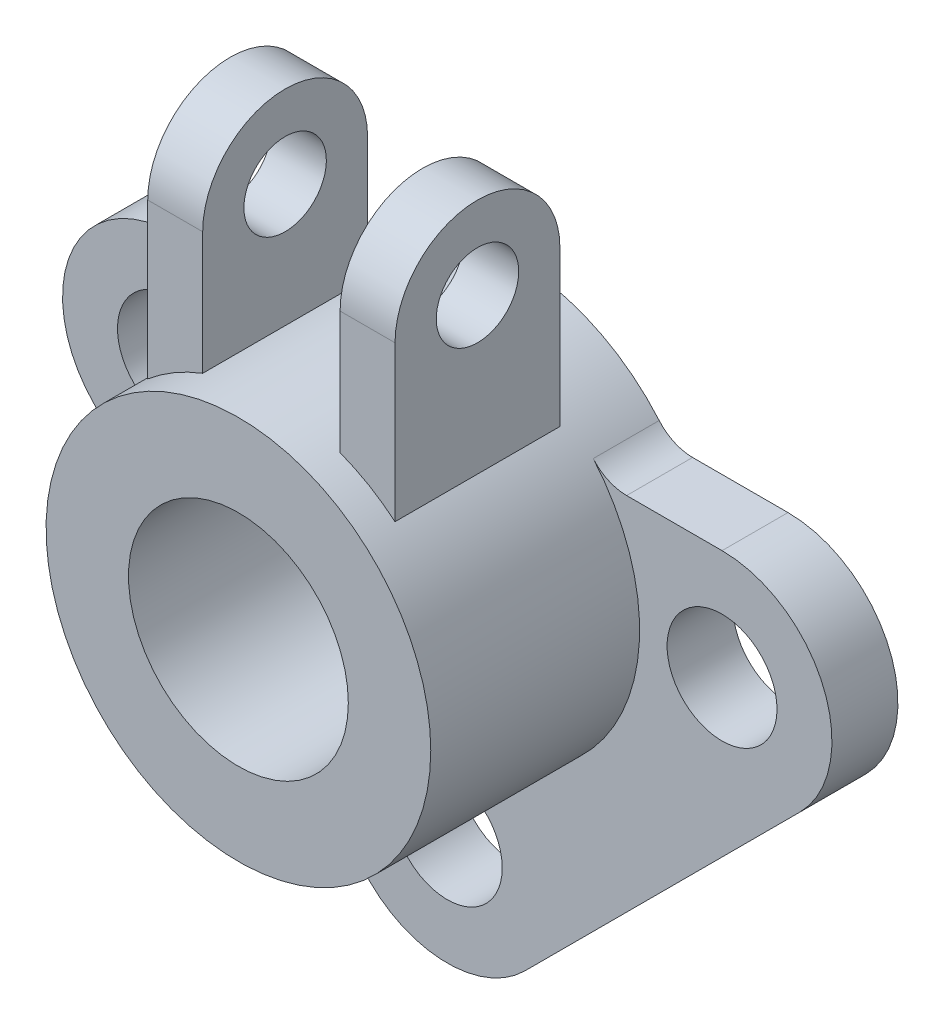
SolidWorks part; units mm, degrees
ref_plane "Front Plane" through (0, 0, 0) normal (0, 0, 1) x (1, 0, 0)
ref_plane "Top Plane" through (0, 0, 0) normal (0, 1, 0) x (1, 0, 0)
ref_plane "Right Plane" through (0, 0, 0) normal (1, 0, 0) x (0, 0, -1)
sketch "Sketch1" plane through (0, 0, 0) normal (0, 0, 1) x (1, 0, 0)
  circle A0 centre (0, 0) radius 350
  circle A1 centre (0, 0) radius 200
  dimension "D1" = 700
  dimension "D2" = 400
extrude "Boss-Extrude1" add sketch "Sketch1" along normal blind 500 contours A0 A1
sketch "Sketch2" plane through (0, 0, 0) normal (0, 0, 1) x (1, 0, 0)
  line L0 (141.4214, -641.4214) -> (641.4214, -141.4214)
  line L1 (500, 200) -> (287.2281, 200)
  line L2 (-141.4214, -641.4214) -> (-641.4214, -141.4214)
  line L3 (-500, 200) -> (-287.2281, 200)
  line L4 (0, 0) -> (0, -500) construction
  circle A0 centre (0, 0) radius 350 construction
  arc A1 (641.4214, -141.4214) -> (500, 200) centre (500, 0) ccw
  arc A2 (141.4214, -641.4214) -> (-141.4214, -641.4214) centre (0, -500) cw
  arc A3 (-641.4214, -141.4214) -> (-500, 200) centre (-500, 0) cw
  circle A4 centre (-500, 0) radius 100
  circle A5 centre (500, 0) radius 100
  circle A6 centre (0, -500) radius 100
  circle A7 centre (0, 0) radius 200 construction
  circle A8 centre (0, 0) radius 200
  circle A9 centre (0, 0) radius 350 construction
  circle A10 centre (0, 0) radius 350
  point P18 (0, -782.8427)
  dimension "D1" = 200
  dimension "D2" = 200
  dimension "D3" = 1000
  dimension "D4" = 500
  dimension "D5" = 500
extrude "Boss-Extrude2" add sketch "Sketch2" along normal blind 120
fillet "Fillet1" radius 80 2 edges at (-287.2281, 200, 60) (287.2281, 200, 60)
sketch "Sketch3" plane through (0, 0, 500) normal (0, 0, 1) x (1, 0, 0)
  line L0 (0, 0) -> (0, 564.9345) construction
  line L1 (225, 700) -> (125, 700)
  line L2 (125, 700) -> (125, 326.9174)
  line L3 (225, 700) -> (225, 268.0951)
  line L4 (-225, 700) -> (-225, 268.0951)
  line L5 (-125, 700) -> (-125, 326.9174)
  line L6 (-225, 700) -> (-125, 700)
  circle A0 centre (0, 0) radius 350 construction
  arc A1 (225, 268.0951) -> (125, 326.9174) centre (0, 0) ccw
  arc A2 (-225, 268.0951) -> (-125, 326.9174) centre (0, 0) cw
  dimension "D1" = 700
  dimension "D2" = 100
  dimension "D3" = 250
extrude "Boss-Extrude3" add sketch "Sketch3" against normal blind 300 from offset 60 offset against normal yes
sketch "Sketch4" plane through (225, 0, 0) normal (1, 0, 0) x (0, 0, -1)
  line L0 (-140, 700) -> (-440, 700) construction
  line L1 (-140, 268.0951) -> (-140, 700) construction
  circle A0 centre (-290, 550) radius 150
  circle A1 centre (-290, 550) radius 75
  line M3 (-440, 700) -> (-440, 268.0951)
  line M5 (-140, 268.0951) -> (-140, 700)
  line M6 (-140, 700) -> (-440, 700)
  dimension "D1" = 300
  dimension "D2" = 150
extrude "Cut-Extrude2" cut sketch "Sketch4" against normal up to surface (450 mm away) contours A0 M6 M3 | A0 M5 M6 | A1 up to face at (-225, 484.0476, 290)
